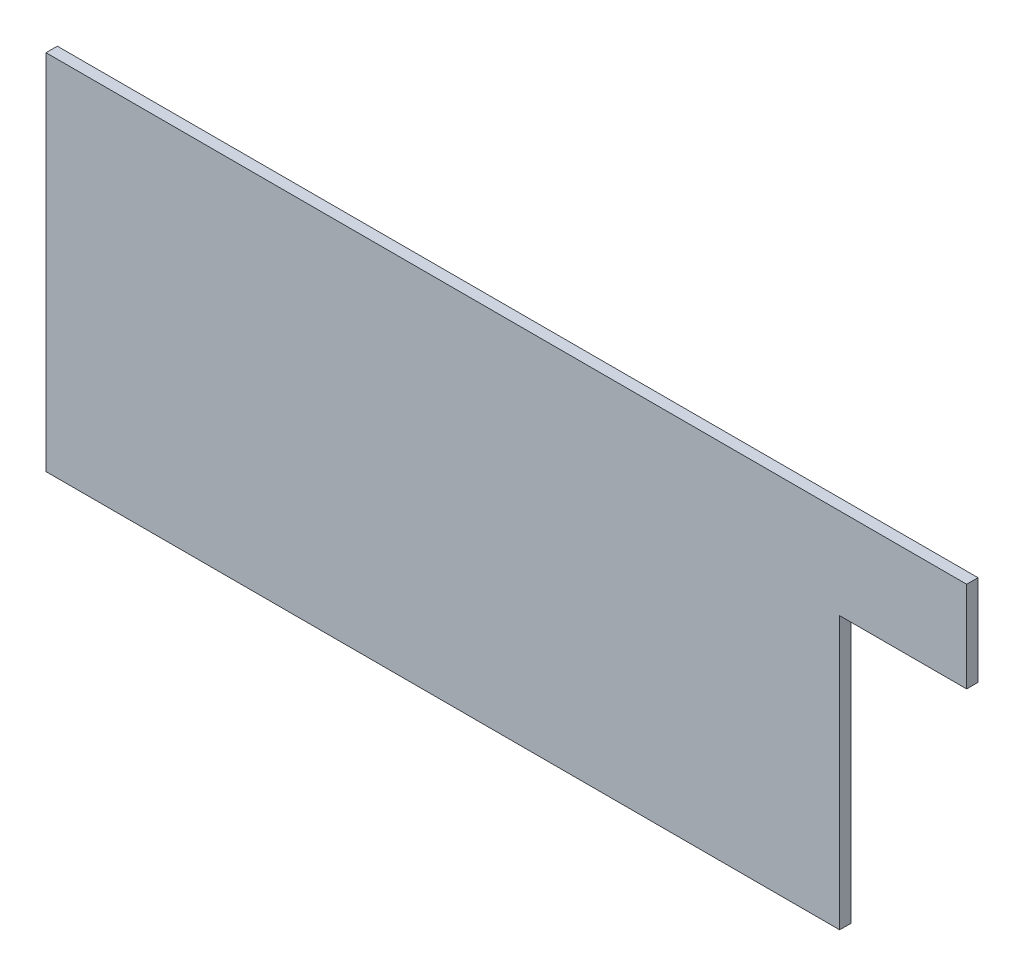
SolidWorks part; units mm, degrees
ref_plane "Front Plane" through (0, 0, 0) normal (0, 0, 1) x (1, 0, 0)
ref_plane "Top Plane" through (0, 0, 0) normal (0, 1, 0) x (1, 0, 0)
ref_plane "Right Plane" through (0, 0, 0) normal (1, 0, 0) x (0, 0, -1)
sketch "Sketch1" plane through (0, 0, 0) normal (0, 0, 1) x (1, 0, 0)
  line L0 (257.81, 76.2) -> (222.25, 76.2)
  line L1 (0, 0) -> (222.25, 0)
  line L2 (0, 0) -> (0, 101.6)
  line L3 (0, 101.6) -> (63.5, 101.6)
  line L4 (257.81, 76.2) -> (257.81, 101.6)
  line L5 (222.25, 76.2) -> (222.25, 0)
  line L9 (165.1, 101.6) -> (257.81, 101.6)
  line L10 (63.5, 101.6) -> (165.1, 101.6)
  dimension "D1" = 257.81
  dimension "D2" = 101.6
  dimension "D3" = 35.56
  dimension "D4" = 76.2
extrude "Boss-Extrude1" add sketch "Sketch1" along normal blind 3.175
